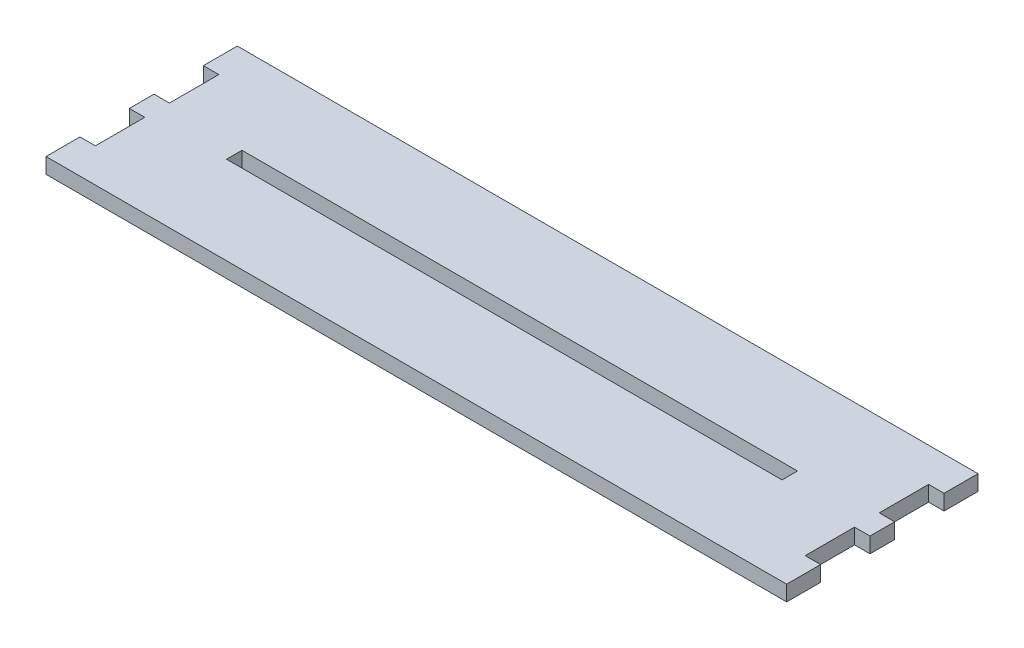
SolidWorks part; units mm, degrees
ref_plane "Front Plane" through (0, 0, 0) normal (0, 0, 1) x (1, 0, 0)
ref_plane "Top Plane" through (0, 0, 0) normal (0, 1, 0) x (1, 0, 0)
ref_plane "Right Plane" through (0, 0, 0) normal (1, 0, 0) x (0, 0, -1)
sketch "Sketch1" plane through (0, 0, 0) normal (0, 1, 0) x (1, 0, 0)
  line L0 (-39.6776, -21.9061) -> (-39.6776, -14.9211) construction
  line L1 (-42.8526, 17.4639) -> (109.5474, 17.4639)
  line L2 (-42.8526, 17.4639) -> (-42.8526, 10.4789)
  line L3 (-42.8526, -21.9061) -> (109.5474, -21.9061)
  line L4 (109.5474, 17.4639) -> (109.5474, 10.4789)
  line L5 (-42.8526, -2.2211) -> (-49.6362, -2.2211) construction
  line L6 (-39.6776, 17.4639) -> (-39.6776, 10.4789) construction
  line L7 (-42.8526, 0.3189) -> (-42.8526, -4.7611)
  line L8 (-39.6776, 10.4789) -> (-42.8526, 10.4789)
  line L9 (-39.6776, 10.4789) -> (-39.6776, 0.3189)
  line L10 (-39.6776, 0.3189) -> (-42.8526, 0.3189)
  line L11 (-39.6776, -4.7611) -> (-42.8526, -4.7611)
  line L12 (-39.6776, -14.9211) -> (-42.8526, -14.9211)
  line L13 (-39.6776, -14.9211) -> (-39.6776, -4.7611)
  line L14 (33.3474, 17.4639) -> (33.3474, -21.9061) construction
  line L15 (106.3724, -14.9211) -> (109.5474, -14.9211)
  line L16 (106.3724, -14.9211) -> (106.3724, -4.7611)
  line L17 (106.3724, -4.7611) -> (109.5474, -4.7611)
  line L18 (106.3724, 0.3189) -> (109.5474, 0.3189)
  line L19 (106.3724, 10.4789) -> (106.3724, 0.3189)
  line L20 (106.3724, 10.4789) -> (109.5474, 10.4789)
  line L21 (-42.8526, -14.9211) -> (-42.8526, -21.9061)
  line L22 (109.5474, -14.9211) -> (109.5474, -21.9061)
  line L23 (109.5474, 0.3189) -> (109.5474, -4.7611)
  dimension "D1" = 39.37
  dimension "D2" = 152.4
  dimension "D4" = 3.175
  dimension "D5" = 10.16
  dimension "D6" = 5.08
extrude "Boss-Extrude1" add sketch "Sketch1" along normal blind 3.175 contours L1 L4 L20 L19 L18 L23 L17 L16 L15 L22 L3 L21 L12 L13 L11 L7 L10 L9 L8 L2
sketch "Sketch2" plane through (0, 3.175, 0) normal (0, 1, 0) x (1, 0, 0)
  line L0 (-42.8526, -2.2211) -> (-23.8026, -2.2211) construction
  line L1 (90.4974, -3.8086) -> (-23.8026, -3.8086)
  line L2 (90.4974, -3.8086) -> (90.4974, -0.6336)
  line L3 (90.4974, -0.6336) -> (-23.8026, -0.6336)
  line L4 (-23.8026, -3.8086) -> (-23.8026, -0.6336)
  line L5 (-42.8526, 0.3189) -> (-42.8526, -4.7611) construction
  line L6 (90.4974, -2.2211) -> (109.5474, -2.2211) construction
  line L7 (109.5474, 0.3189) -> (109.5474, -4.7611) construction
  line L8 (33.3474, -0.6336) -> (33.3474, 17.4639) construction
  line L9 (-42.8526, 17.4639) -> (109.5474, 17.4639) construction
  line L10 (33.3474, -3.8086) -> (33.3474, -21.9061) construction
  line L11 (-42.8526, -21.9061) -> (109.5474, -21.9061) construction
  dimension "D1" = 3.175
  dimension "D2" = 114.3
extrude "Cut-Extrude1" cut sketch "Sketch2" against normal through all
